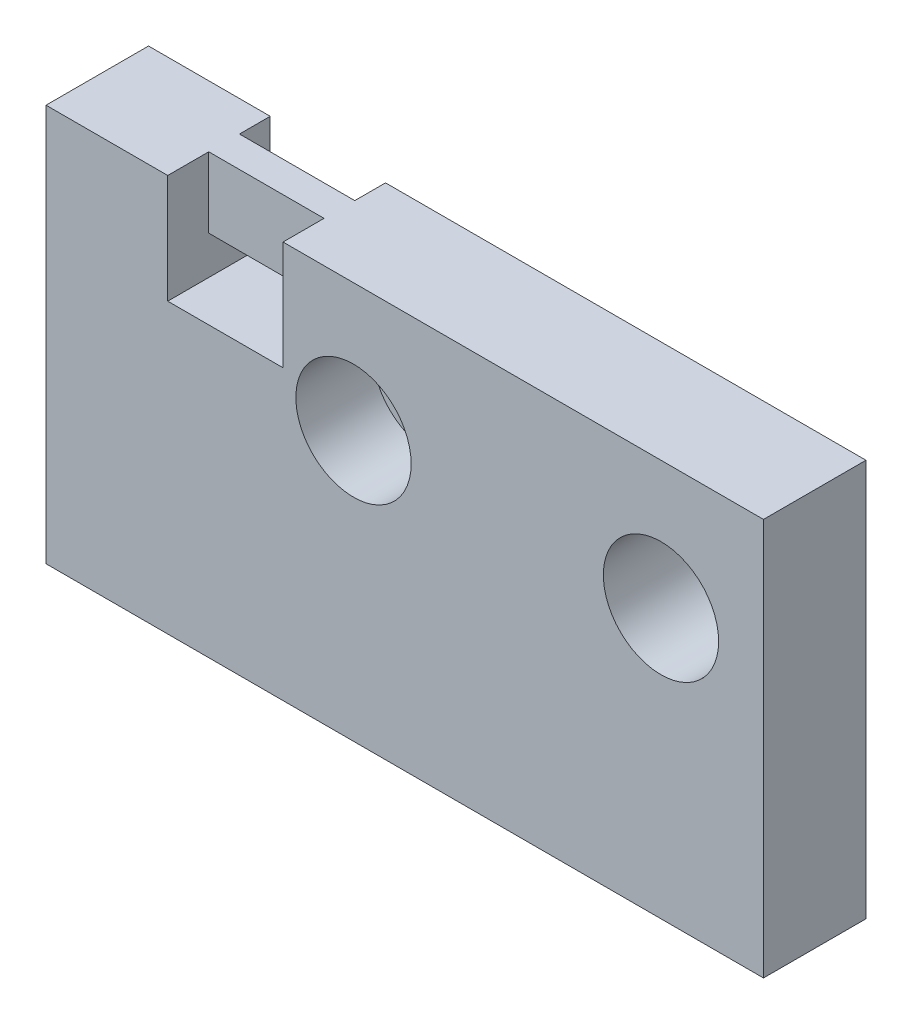
SolidWorks part; units mm, degrees
ref_plane "Front Plane" through (0, 0, 0) normal (0, 0, 1) x (1, 0, 0)
ref_plane "Top Plane" through (0, 0, 0) normal (0, 1, 0) x (1, 0, 0)
ref_plane "Right Plane" through (0, 0, 0) normal (1, 0, 0) x (0, 0, -1)
sketch "Sketch1" plane through (0, 0, 0) normal (0, 0, 1) x (1, 0, 0)
  line L1 (0, 0) -> (28, 0)
  line L2 (0, 0) -> (0, -15.5)
  line L3 (0, -15.5) -> (28, -15.5)
  line L4 (28, 0) -> (28, -15.5)
extrude "Boss-Extrude1" add sketch "Sketch1" along normal blind 4
sketch "Sketch2" plane through (0, 0, 4) normal (0, 0, 1) x (1, 0, 0)
  circle A0 centre (12, -5) radius 1.25
  circle A1 centre (24, -5) radius 1.25
extrude "Cut-Extrude1" cut sketch "Sketch2" against normal blind 4
sketch "Sketch3" plane through (0, 0, 4) normal (0, 0, 1) x (1, 0, 0)
  circle A0 centre (12, -5) radius 2.25
  circle A1 centre (24, -5) radius 2.25
extrude "Cut-Extrude2" cut sketch "Sketch3" against normal blind 3
sketch "Sketch4" plane through (0, 0, 4) normal (0, 0, 1) x (1, 0, 0)
  line L6 (9.25, 0.25) -> (9.25, -4.25)
  line L7 (9.25, -4.25) -> (4.75, -4.25)
  line L8 (4.75, -4.25) -> (4.75, 0.25)
  line L9 (4.75, 0.25) -> (9.25, 0.25)
extrude "Cut-Extrude3" cut sketch "Sketch4" against normal blind 1.6
sketch "Sketch5" plane through (0, 0, 2.4) normal (0, 0, 1) x (1, 0, 0)
  line L0 (9.25, -4.25) -> (9.25, 0) construction
  line L1 (4.75, -4.25) -> (9.25, -4.25)
  line L2 (4.75, -4.25) -> (4.75, -2.75)
  line L3 (4.75, -2.75) -> (9.25, -2.75)
  line L4 (9.25, -4.25) -> (9.25, -2.75)
extrude "Cut-Extrude4" cut sketch "Sketch5" against normal blind 4
sketch "Sketch6" plane through (0, 0, 0) normal (0, 0, -1) x (-1, 0, 0)
  line L0 (-28, 0) -> (0, 0) construction
  line L1 (-9.25, -4.25) -> (-4.75, -4.25)
  line L2 (-9.25, -4.25) -> (-9.25, 0)
  line L3 (-9.25, 0) -> (-4.75, 0)
  line L4 (-4.75, -4.25) -> (-4.75, 0)
extrude "Cut-Extrude5" cut sketch "Sketch6" against normal blind 1.2
sketch "Sketch7" plane through (0, 0, 4) normal (0, 0, 1) x (1, 0, 0)
  circle A0 centre (24, -5) radius 2.25
extrude "Cut-Extrude6" cut sketch "Sketch7" against normal blind 10
